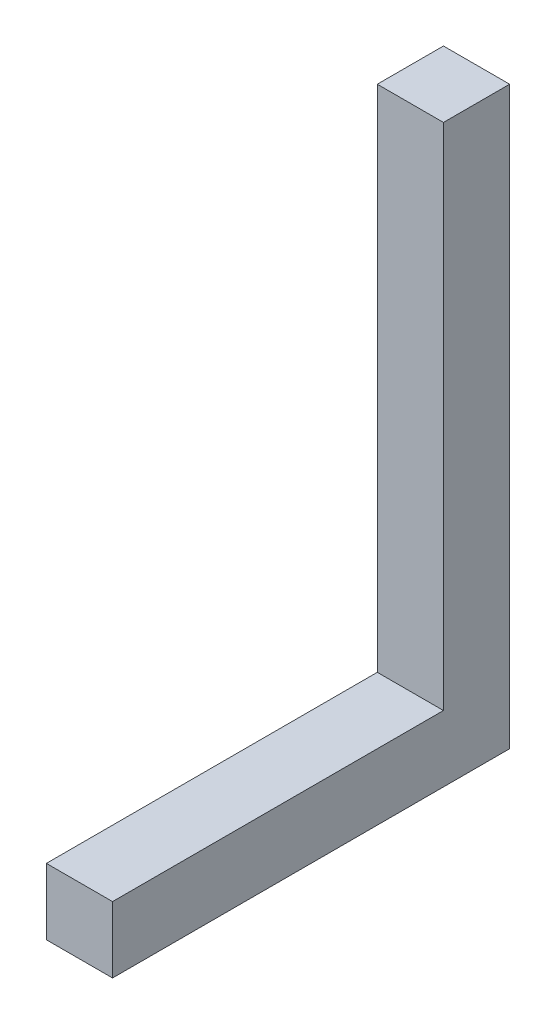
SolidWorks part; units mm, degrees
ref_plane "Front Plane" through (0, 0, 0) normal (0, 0, 1) x (1, 0, 0)
ref_plane "Top Plane" through (0, 0, 0) normal (0, 1, 0) x (1, 0, 0)
ref_plane "Right Plane" through (0, 0, 0) normal (1, 0, 0) x (0, 0, -1)
sketch "Sketch1" plane through (0, 0, 0) normal (0, 0, 1) x (1, 0, 0)
  line L1 (5.75, 5.75) -> (-5.75, 5.75)
  line L2 (5.75, 5.75) -> (5.75, -5.75)
  line L3 (5.75, -5.75) -> (-5.75, -5.75)
  line L4 (-5.75, 5.75) -> (-5.75, -5.75)
  line L5 (5.75, 5.75) -> (-5.75, -5.75) construction
  line L6 (5.75, -5.75) -> (-5.75, 5.75) construction
  point P0 (0, 0)
  dimension "D1" = 11.5
  dimension "D2" = 11.5
extrude "Boss-Extrude1" add sketch "Sketch1" along normal blind 57.5
sketch "Sketch2" plane through (0, 0, 0) normal (0, 1, 0) x (1, 0, 0)
  line L1 (5.75, 0) -> (-5.75, 0)
  line L2 (5.75, 0) -> (5.75, 11.5)
  line L3 (5.75, 11.5) -> (-5.75, 11.5)
  line L4 (-5.75, 0) -> (-5.75, 11.5)
  dimension "D1" = 11.5
  dimension "D2" = 11.5
extrude "Boss-Extrude2" add sketch "Sketch2" along normal blind 100 from surface at -5.75 starting at face at (0, -5.75, 28.75)
